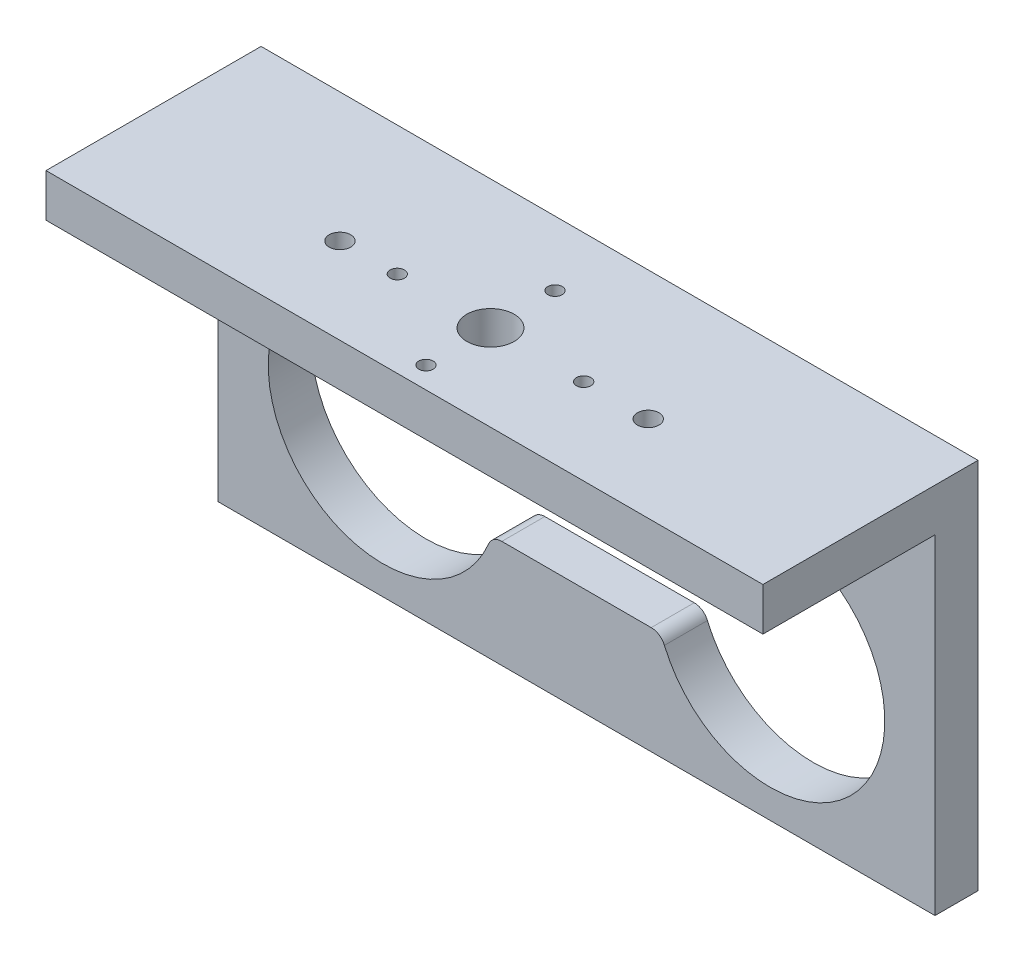
SolidWorks part; units mm, degrees
other "标注1"
sketch "草图6" plane through (25, -10, 15) normal (0.0929, -0.9273, 0.3626) x (0.5024, 0.3581, 0.787)
other "标注2"
sketch "草图7" plane through (25, -10, 15) normal (0.0929, -0.9273, 0.3626) x (0.5024, 0.3581, 0.787)
other "标注3"
sketch "草图8" plane through (25, -10, 15) normal (0.0929, -0.9273, 0.3626) x (0.5024, 0.3581, 0.787)
ref_plane "前视基准面" through (0, 0, 0) normal (0, 0, 1) x (1, 0, 0)
ref_plane "上视基准面" through (0, 0, 0) normal (0, 1, 0) x (1, 0, 0)
ref_plane "右视基准面" through (0, 0, 0) normal (1, 0, 0) x (0, 0, -1)
sketch "草图1" plane through (0, 0, 0) normal (0, 0, 1) x (1, 0, 0)
  line L1 (25, -10) -> (-25, -10)
  line L2 (25, -10) -> (25, 10)
  line L3 (25, 10) -> (-25, 10)
  line L4 (-25, -10) -> (-25, 10)
  line L5 (25, -10) -> (-25, 10) construction
  line L6 (25, 10) -> (-25, -10) construction
  line L8 (-5.2084, 2.5) -> (5.2084, 2.5)
  line L9 (5.2084, -2.5) -> (-5.2084, -2.5)
  line L10 (3.25, 7.25) -> (-3.25, 7.25) construction
  line L11 (3.25, 5.5) -> (-3.25, 5.5)
  line L12 (3.25, 9) -> (-3.25, 9)
  arc A7 (6.1297, -3.1111) -> (6.1297, 3.1111) centre (13.5, 0) ccw
  arc A8 (-6.1297, 3.1111) -> (-6.1297, -3.1111) centre (-13.5, 0) ccw
  arc A9 (5.2084, -2.5) -> (6.1297, -3.1111) centre (5.2084, -3.5) cw
  arc A10 (5.2084, 2.5) -> (6.1297, 3.1111) centre (5.2084, 3.5) ccw
  arc A11 (-5.2084, -2.5) -> (-6.1297, -3.1111) centre (-5.2084, -3.5) ccw
  arc A12 (-5.2084, 2.5) -> (-6.1297, 3.1111) centre (-5.2084, 3.5) cw
  arc A13 (3.25, 5.5) -> (3.25, 9) centre (3.25, 7.25) ccw
  arc A14 (-3.25, 9) -> (-3.25, 5.5) centre (-3.25, 7.25) ccw
  point P0 (0, 0)
  point P22 (0, 7.25)
  dimension "D3" = 1
  dimension "D4" = 8
  dimension "D5" = 8
  dimension "D6" = 2.5
  dimension "D8" = 13.5
  dimension "D9" = 13.5
  dimension "D12" = 1.75
  dimension "D1" = 20
  dimension "D2" = 50
  dimension "D7" = 2.5
  dimension "D10" = 7.25
  dimension "D11" = 6.5
  dimension "D13" = 3.25
extrude "凸台-拉伸1" add sketch "草图1" along normal blind 3
sketch "草图2" plane through (0, 10, 0) normal (0, 1, 0) x (1, 0, 0)
  line L1 (-25, 0) -> (25, 0)
  line L2 (-25, 0) -> (-25, -15)
  line L3 (-25, -15) -> (25, -15)
  line L4 (25, 0) -> (25, -15)
  dimension "D1" = 15
extrude "凸台-拉伸2" add sketch "草图2" along normal blind 6
sketch "草图5" plane through (0, 10, 0) normal (0, -1, 0) x (1, 0, 0)
  line L1 (25, 3) -> (-25, 3)
  line L2 (25, 3) -> (25, 15)
  line L3 (25, 15) -> (-25, 15)
  line L4 (-25, 3) -> (-25, 15)
extrude "切除-拉伸2" cut sketch "草图5" against normal blind 3
sketch "草图4" plane through (0, 16, 0) normal (0, 1, 0) x (1, 0, 0)
  line L0 (-25, -15) -> (25, -15) construction
  circle A0 centre (0, -9) radius 1.65
  circle A1 centre (6.5, -9) radius 0.5
  circle A2 centre (-6.5, -9) radius 0.5
  circle A3 centre (11, -9) radius 0.75
  circle A4 centre (-10.5, -9) radius 0.75
  circle A5 centre (0, -4.5) radius 0.5
  circle A6 centre (0, -13.5) radius 0.5
  dimension "D1" = 3.3
  dimension "D2" = 1
  dimension "D3" = 6.5
  dimension "D4" = 1
  dimension "D5" = 6.5
  dimension "D6" = 6
  dimension "D7" = 1.5
  dimension "D8" = 1.5
  dimension "D9" = 10.5
  dimension "D10" = 11
  dimension "D11" = 1
  dimension "D12" = 1
  dimension "D13" = 4.5
  dimension "D14" = 4.5
extrude "切除-拉伸1" cut sketch "草图4" against normal up to surface (3 mm away) up to face at (0, 13, 9)
sketch "草图10" plane through (0, 16, 0) normal (0, 1, 0) x (1, 0, 0)
  line L0 (-25, 0) -> (-25, -15) construction
  line L1 (25, 0) -> (-25, 0)
  line L2 (25, 0) -> (25, -3)
  line L3 (25, -3) -> (-25, -3)
  line L4 (-25, 0) -> (-25, -3)
